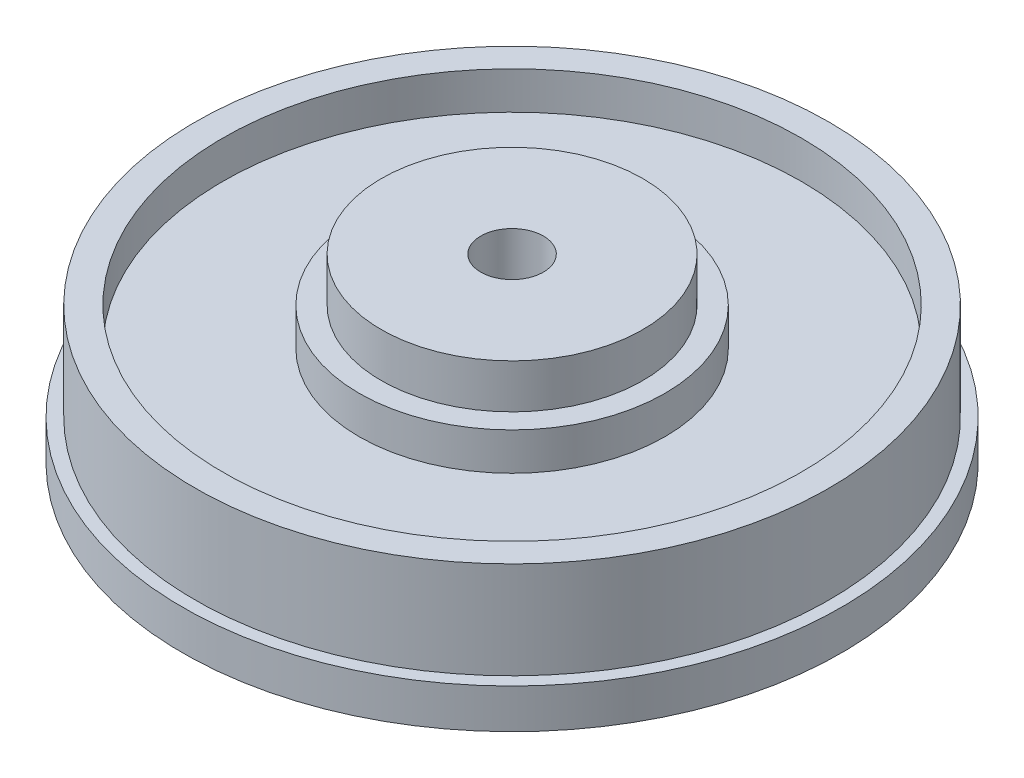
SolidWorks part; units mm, degrees
ref_plane "Plano frontal" through (0, 0, 0) normal (0, 0, 1) x (1, 0, 0)
ref_plane "Plano superior" through (0, 0, 0) normal (0, 1, 0) x (1, 0, 0)
ref_plane "Plano direito" through (0, 0, 0) normal (1, 0, 0) x (0, 0, -1)
sketch "Esboço1" plane through (0, 0, 0) normal (0, 0, 1) x (1, 0, 0)
  line L0 (0, 0) -> (0, 8.3592) construction
  line L1 (4.75, 0) -> (4.75, 27.4)
  line L2 (4.75, 27.4) -> (19.85, 27.4)
  line L3 (19.85, 27.4) -> (19.85, 20.7)
  line L4 (19.85, 20.7) -> (23.2, 20.7)
  line L5 (23.2, 20.7) -> (23.2, 15)
  line L6 (23.2, 15) -> (43.9, 15)
  line L7 (43.9, 15) -> (43.9, 20.7)
  line L8 (43.9, 20.7) -> (48.1, 20.7)
  line L9 (48.1, 20.7) -> (48.1, 6)
  line L10 (48.1, 6) -> (50, 6)
  line L11 (50, 6) -> (50, 0)
  line L12 (50, 0) -> (39.85, 0)
  line L13 (19.85, 0) -> (19.85, 2)
  line L14 (19.85, 2) -> (39.85, 2)
  line L15 (39.85, 2) -> (39.85, 0)
  line L16 (19.85, 0) -> (4.75, 0)
  point P17 (51.2345, 0.3548)
  point P20 (4.75, 22.4712)
  point P21 (4.75, 0)
  point P22 (24.3197, 0.3731)
  point P23 (41.5007, 0)
  dimension "D1" = 9.5
  dimension "D2" = 6
  dimension "D3" = 14.7
  dimension "D4" = 39.7
  dimension "D5" = 46.4
  dimension "D6" = 87.8
  dimension "D7" = 96.2
  dimension "D8" = 5.7
  dimension "D9" = 6.7
  dimension "D10" = 2
  dimension "D11" = 20
  dimension "D12" = 100
revolve "Revolução1" add sketch "Esboço1" angle 360 about L0
